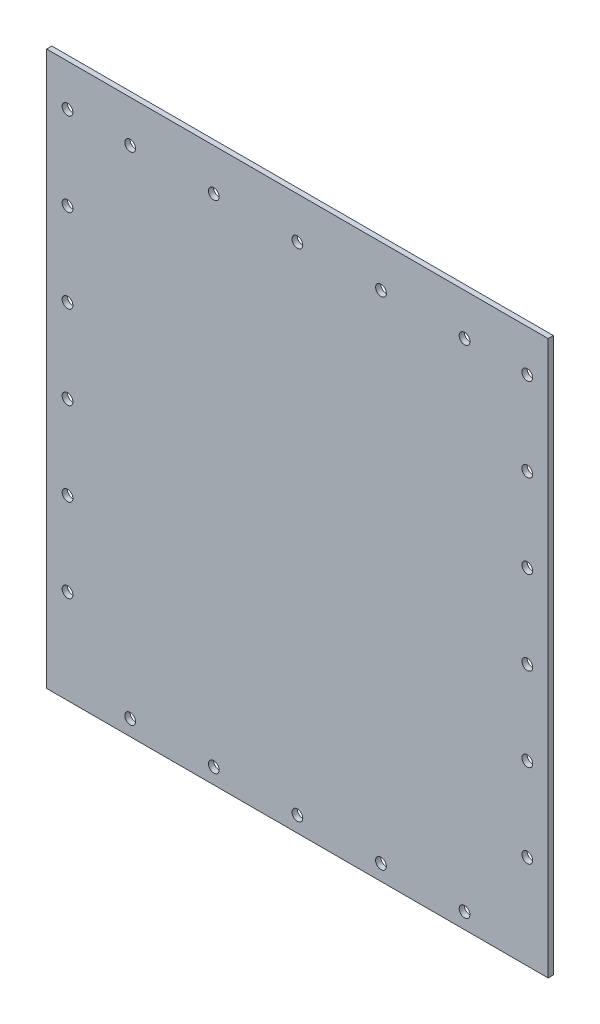
SolidWorks part; units mm, degrees
material "Copper"
ref_plane "Front Plane" through (0, 0, 0) normal (0, 0, 1) x (1, 0, 0)
ref_plane "Top Plane" through (0, 0, 0) normal (0, 1, 0) x (1, 0, 0)
ref_plane "Right Plane" through (0, 0, 0) normal (1, 0, 0) x (0, 0, -1)
sketch "Sketch1" plane through (0, 0, 0) normal (0, 0, 1) x (1, 0, 0)
  line L0 (0, -100.6) -> (152.4, -100.6)
  line L1 (0, 0) -> (152.4, 0)
  line L2 (0, 0) -> (0, -269.8716)
  line L3 (0, -269.8716) -> (152.4, -269.8716)
  line L4 (152.4, 0) -> (152.4, -269.8716)
  line L5 (0, -101.6) -> (152.4, -101.6)
  circle A0 centre (6.35, -12.7) radius 1.632
  circle A1 centre (146.05, -12.7) radius 1.632
  circle A2 centre (146.05, -38.1) radius 1.632
  circle A3 centre (146.05, -63.5) radius 1.632
  circle A4 centre (146.05, -88.9) radius 1.632
  circle A5 centre (146.05, -114.3) radius 1.632
  circle A6 centre (146.05, -139.7) radius 1.632
  circle A7 centre (146.05, -165.1) radius 1.632
  circle A8 centre (146.05, -190.5) radius 1.632
  circle A9 centre (146.05, -215.9) radius 1.632
  circle A10 centre (146.05, -241.3) radius 1.632
  circle A11 centre (6.35, -38.1) radius 1.6319
  circle A12 centre (6.35, -63.5) radius 1.6319
  circle A13 centre (6.35, -88.9) radius 1.6319
  circle A14 centre (6.35, -114.3) radius 1.6319
  circle A15 centre (6.35, -139.7) radius 1.632
  circle A16 centre (6.35, -165.1) radius 1.632
  circle A17 centre (6.35, -190.5) radius 1.632
  circle A18 centre (6.35, -215.9) radius 1.632
  circle A19 centre (6.35, -241.3) radius 1.632
  circle A20 centre (12.7, -3.175) radius 1.632
  circle A21 centre (38.1, -3.175) radius 1.632
  circle A22 centre (63.5, -3.175) radius 1.632
  circle A23 centre (88.9, -3.175) radius 1.632
  circle A24 centre (114.3, -3.175) radius 1.632
  circle A25 centre (139.7, -3.175) radius 1.632
  circle A26 centre (25.4, -265.1125) radius 1.632
  circle A27 centre (50.8, -265.1125) radius 1.632
  circle A28 centre (76.2, -265.1125) radius 1.632
  circle A29 centre (101.6, -265.1125) radius 1.632
  circle A30 centre (127, -265.1125) radius 1.632
  circle A31 centre (25.4, -88.9) radius 1.6319
  circle A32 centre (25.4, -114.3) radius 1.6319
  circle A33 centre (50.8, -114.3) radius 1.6319
  circle A34 centre (50.8, -88.9) radius 1.6319
  circle A35 centre (76.2, -114.3) radius 1.632
  circle A36 centre (76.2, -88.9) radius 1.632
  circle A37 centre (101.6, -114.3) radius 1.632
  circle A38 centre (101.6, -88.9) radius 1.632
  circle A39 centre (127, -114.3) radius 1.632
  circle A40 centre (127, -88.9) radius 1.632
  point P4 (6.6863, 0)
  dimension "D3" = 3.2639
  dimension "D1" = 269.8716
  dimension "D2" = 152.4
  dimension "D4" = 12.7
  dimension "D5" = 6.35
  dimension "D8" = 6.35
  dimension "D9" = 25.4
  dimension "D10" = 3.175
  dimension "D11" = 12.7
  dimension "D13" = 25.4
  dimension "D14" = 4.7591
  dimension "D15" = 25.4
  dimension "D17" = 25.4
  dimension "D18" = 11.7
  dimension "D19" = 1
  dimension "D20" = 25.4
  dimension "D22" = 25.4
  dimension "D6" = 2
  dimension "D7" = 10
  dimension "D12" = 6
  dimension "D16" = 5
  dimension "D21" = 5
extrude "Boss-Extrude1" add sketch "Sketch1" along normal blind 1.5875 contours L5 L2 L3 L4 A39 A37 A35 A33 A32 A30 A29 A28 A27 A26 A19 A18 A17 A16 A15 A14 A10 A9 A8 A7 A6 A5
